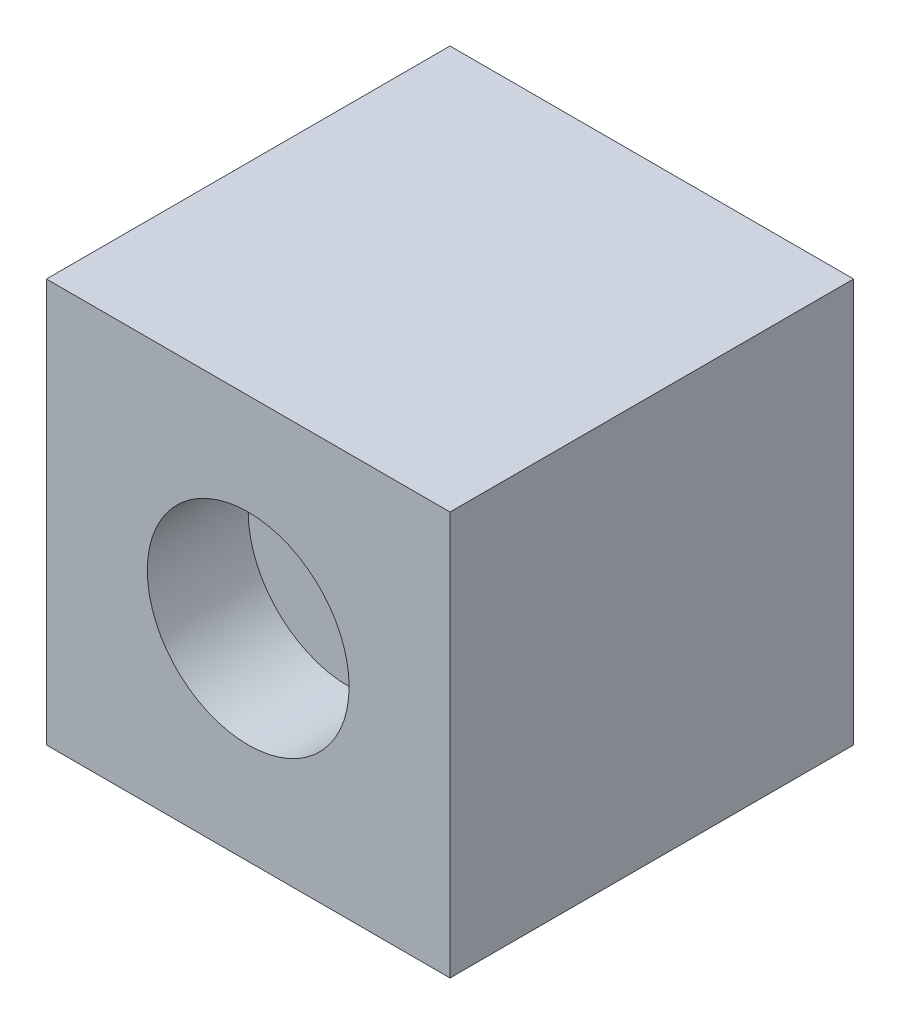
SolidWorks part; units mm, degrees
ref_plane "Front" through (0, 0, 0) normal (0, 0, 1) x (1, 0, 0)
ref_plane "Top" through (0, 0, 0) normal (0, 1, 0) x (1, 0, 0)
ref_plane "Right" through (0, 0, 0) normal (1, 0, 0) x (0, 0, -1)
sketch "Sketch2" plane through (0, 0, 0) normal (0, 0, 1) x (1, 0, 0)
  line L1 (-25.4, 25.4) -> (25.4, 25.4)
  line L2 (-25.4, 25.4) -> (-25.4, -25.4)
  line L3 (-25.4, -25.4) -> (25.4, -25.4)
  line L4 (25.4, 25.4) -> (25.4, -25.4)
  dimension "D1" = 50.8
  dimension "D2" = 50.8
  dimension "D3" = 25.4
  dimension "D4" = 25.4
extrude "Boss-Extrude1" add sketch "Sketch2" along normal blind 50.8
sketch "Sketch3" plane through (0, 0, 50.8) normal (0, 0, 1) x (1, 0, 0)
  circle A0 centre (0, 0) radius 12.7
  dimension "D1" = 25.4
extrude "Cut-Extrude1" cut sketch "Sketch3" against normal blind 12.7
